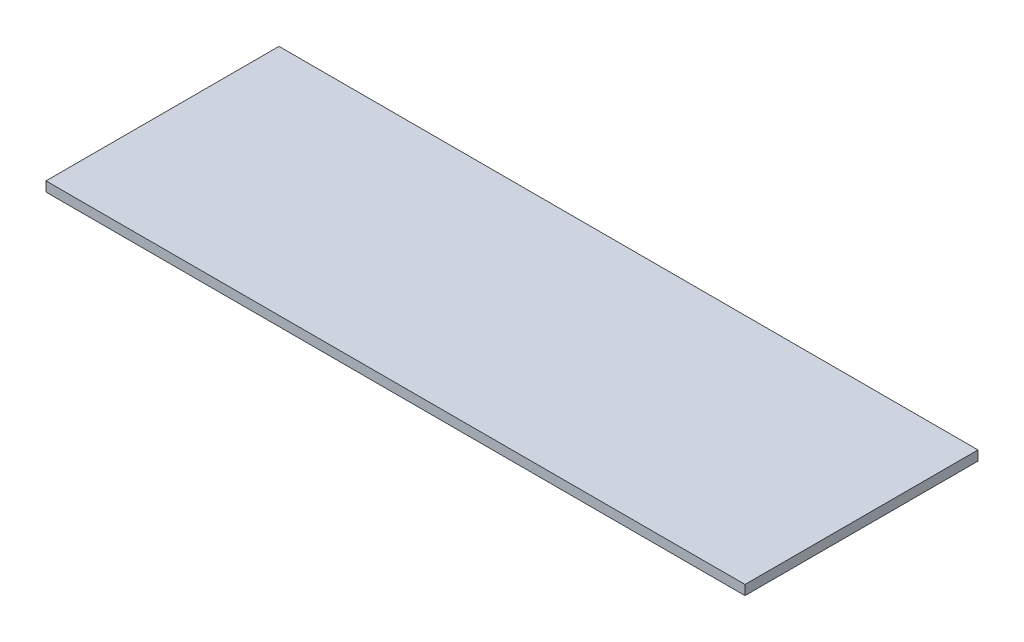
SolidWorks part; units mm, degrees
ref_plane "Front Plane" through (0, 0, 0) normal (0, 0, 1) x (1, 0, 0)
ref_plane "Top Plane" through (0, 0, 0) normal (0, 1, 0) x (1, 0, 0)
ref_plane "Right Plane" through (0, 0, 0) normal (1, 0, 0) x (0, 0, -1)
sketch "Sketch1" plane through (0, 0, 0) normal (0, 1, 0) x (1, 0, 0)
  line L1 (905.3417, 323.6453) -> (-894.6583, 323.6453)
  line L2 (905.3417, 323.6453) -> (905.3417, -276.3547)
  line L3 (905.3417, -276.3547) -> (-894.6583, -276.3547)
  line L4 (-894.6583, 323.6453) -> (-894.6583, -276.3547)
  dimension "D1" = 1800
  dimension "D2" = 600
extrude "Boss-Extrude1" add sketch "Sketch1" along normal blind 25
